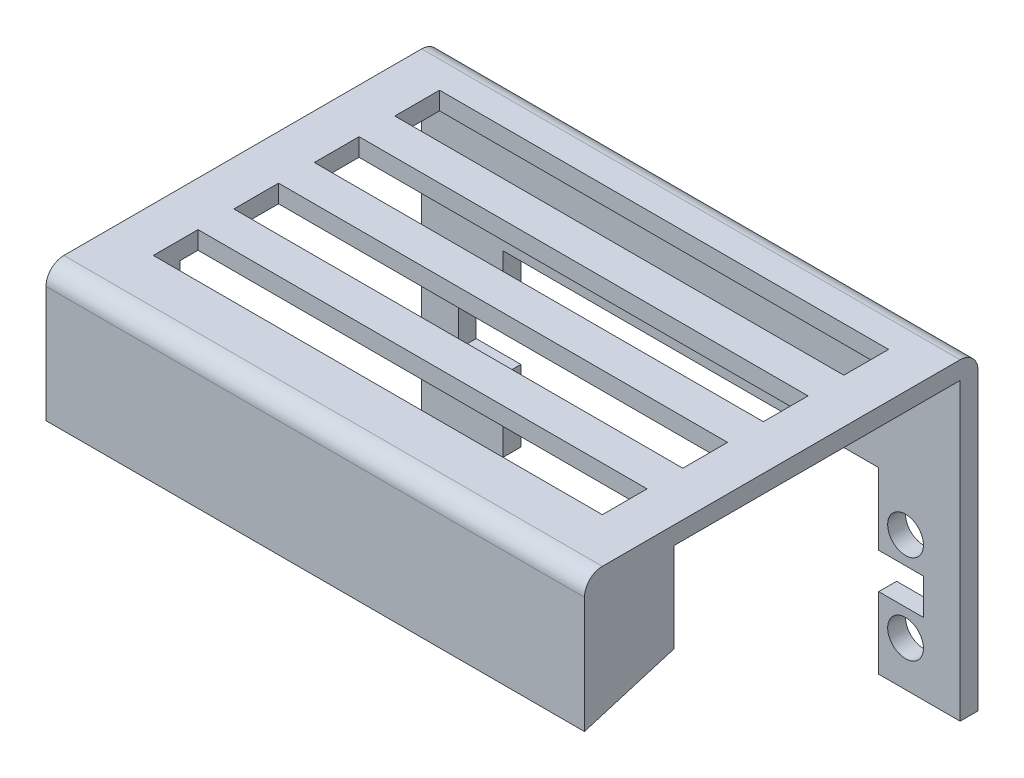
SolidWorks part; units mm, degrees
material "PET-G 50%"
ref_plane "Front Plane" through (0, 0, 0) normal (0, 0, 1) x (1, 0, 0)
ref_plane "Top Plane" through (0, 0, 0) normal (0, 1, 0) x (1, 0, 0)
ref_plane "Right Plane" through (0, 0, 0) normal (1, 0, 0) x (0, 0, -1)
sketch "Sketch1" plane through (0, 0, 0) normal (1, 0, 0) x (0, 0, -1)
  line L0 (0, 0) -> (0, 15)
  line L1 (0, 15) -> (44, 15)
  line L2 (44, 15) -> (44, -20)
  line L3 (44, -20) -> (42, -20)
  line L4 (42, -20) -> (42, 13)
  line L6 (42, 13) -> (10, 13)
  line L8 (10, 13) -> (10, 3)
  line L9 (10, 3) -> (0, 0)
  dimension "D1" = 44
  dimension "D2" = 10
  dimension "D3" = 3
  dimension "D4" = 2
  dimension "D5" = 23
  dimension "D6" = 10
  dimension "D7" = 2
extrude "Boss-Extrude1" add sketch "Sketch1" against normal blind 60.2
sketch "Sketch3" plane through (0, 0, -44) normal (0, 0, -1) x (-1, 0, 0)
  line L0 (60.2, -20) -> (60.2, 15) construction
  line L1 (60.2, -20) -> (0, -20) construction
  line L2 (0, -20) -> (0, 15) construction
  line L3 (9.1, -8) -> (9.1, 0)
  line L4 (9.1, -20) -> (51.1, -20)
  line L6 (9.1, 0) -> (51.1, 0)
  line L8 (9.1, -8) -> (4.1, -8)
  line L10 (9.1, -12) -> (4.1, -12)
  line L11 (4.1, -8) -> (4.1, -12)
  line L12 (51.1, -8) -> (56.1, -8)
  line L14 (51.1, -12) -> (56.1, -12)
  line L15 (56.1, -8) -> (56.1, -12)
  line L16 (9.1, -12) -> (9.1, -20)
  line L17 (51.1, 0) -> (51.1, -8)
  line L18 (51.1, -12) -> (51.1, -20)
  circle A0 centre (54.1, -15) radius 2
  circle A1 centre (54.1, -5) radius 2
  circle A2 centre (6.1, -15) radius 2
  circle A3 centre (6.1, -5) radius 2
  dimension "D1" = 4
  dimension "D7" = 3
  dimension "D2" = 10
  dimension "D3" = 6.1
  dimension "D4" = 5
  dimension "D5" = 6.1
  dimension "D6" = 20
  dimension "D8" = 3
  dimension "D9" = 4
  dimension "D10" = 5
  dimension "D11" = 3
  dimension "D12" = 4
  dimension "D13" = 5
  dimension "D14" = 3
extrude "Cut-Extrude1" cut sketch "Sketch3" against normal blind 20
sketch "Sketch4" plane through (0, 15, 0) normal (0, 1, 0) x (1, 0, 0)
  line L0 (-60.2, 44) -> (0, 44) construction
  line L1 (-55.2, 39) -> (-5, 39)
  line L2 (-55.2, 39) -> (-55.2, 34)
  line L3 (-55.2, 34) -> (-5, 34)
  line L4 (-5, 39) -> (-5, 34)
  line L5 (-60.2, 44) -> (-60.2, 0) construction
  line L6 (0, 44) -> (0, 0) construction
  dimension "D1" = 5
  dimension "D2" = 5
  dimension "D3" = 5
  dimension "D4" = 5
extrude "Cut-Extrude2" cut sketch "Sketch4" against normal blind 20
pattern_linear "LPattern1" count 4 spacing 9 along (0, 0, 1) of "Cut-Extrude2"
fillet "Fillet1" radius 2 2 edges at (-30.1, 15, 0) (-30.1, 15, -44)
